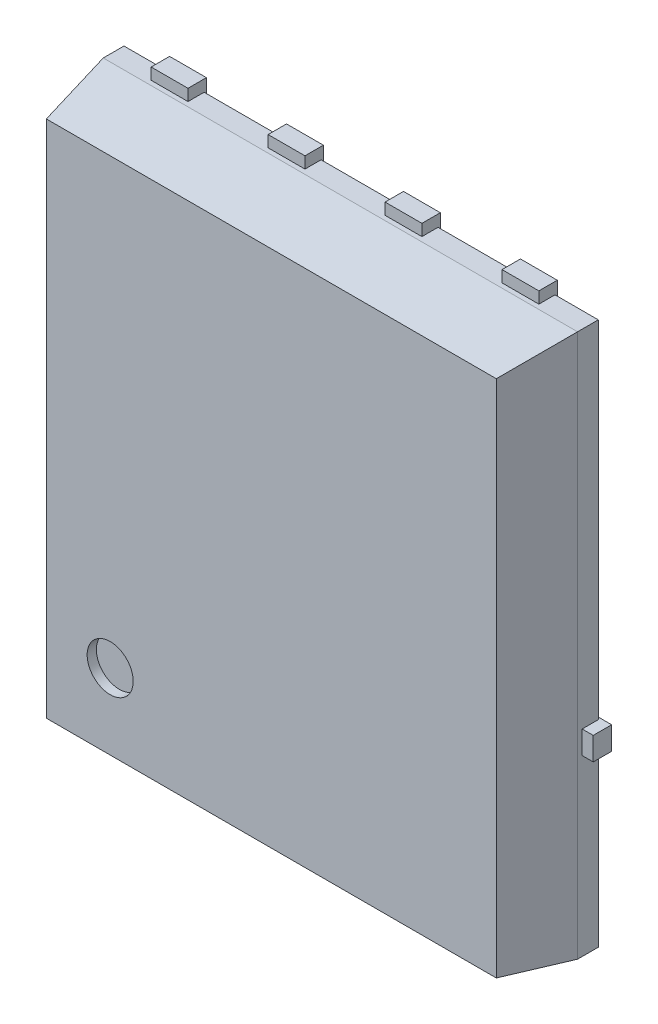
SolidWorks part; units mm, degrees
ref_plane "Plano frontal" through (0, 0, 0) normal (0, 0, 1) x (1, 0, 0)
ref_plane "Plano superior" through (0, 0, 0) normal (0, 1, 0) x (1, 0, 0)
ref_plane "Plano direito" through (0, 0, 0) normal (1, 0, 0) x (0, 0, -1)
sketch "Esboço3" plane through (0, 0, 0) normal (0, 0, 1) x (1, 0, 0)
  line L0 (0, -3.1767) -> (0, 3.1767) construction
  line L1 (-2.575, 2.95) -> (2.575, 2.95)
  line L2 (-2.575, 2.95) -> (-2.575, -2.95)
  line L3 (-2.575, -2.95) -> (2.575, -2.95)
  line L4 (2.575, 2.95) -> (2.575, -2.95)
  line L5 (3.0012, 0) -> (-2.8534, 0) construction
  point P7 (0, 0)
  point P8 (0, 2.95)
  point P11 (2.575, 0)
sketch "Esboço1" plane through (0, 0, 0) normal (0, 0, 1) x (1, 0, 0)
  line L0 (-0.435, 3.075) -> (-0.835, 3.075)
  line L1 (0, -3.5) -> (0, 3.5) construction
  line L2 (3.7953, 0) -> (-3.7953, 0) construction
  line L3 (4.6144, 3.075) -> (-4.6144, 3.075) construction
  line L4 (-1.705, 3.075) -> (-2.105, 3.075)
  line L5 (-0.435, 3.075) -> (-0.435, 2.775)
  line L6 (2.695, -1.06) -> (-2.695, -1.06)
  line L7 (-2.695, -1.06) -> (-2.695, -0.81)
  line L8 (3.5115, 2.525) -> (-3.5115, 2.525) construction
  line L9 (-0.835, 3.075) -> (-0.835, 2.775)
  line L10 (-1.085, 2.525) -> (-1.455, 2.525)
  line L11 (-1.705, 2.775) -> (-1.705, 3.075)
  line L12 (-2.105, 3.075) -> (-2.105, -0.56)
  line L13 (-2.355, -0.81) -> (-2.695, -0.81)
  line L14 (-0.185, 2.525) -> (0.185, 2.525)
  line L15 (2.355, -0.81) -> (2.695, -0.81)
  line L16 (2.105, 3.075) -> (2.105, -0.56)
  line L17 (1.705, 2.775) -> (1.705, 3.075)
  line L18 (1.085, 2.525) -> (1.455, 2.525)
  line L19 (0.835, 3.075) -> (0.835, 2.775)
  line L20 (2.695, -1.06) -> (2.695, -0.81)
  line L21 (0.435, 3.075) -> (0.435, 2.775)
  line L22 (1.705, 3.075) -> (2.105, 3.075)
  line L23 (0.435, 3.075) -> (0.835, 3.075)
  line L24 (0.435, -3.075) -> (0.835, -3.075)
  line L25 (1.705, -3.075) -> (2.105, -3.075)
  line L26 (-1.705, -3.075) -> (-2.105, -3.075)
  line L27 (-0.435, -3.075) -> (-0.835, -3.075)
  line L28 (-2.105, -3.075) -> (-2.105, -2.525)
  line L29 (-2.105, -2.525) -> (-1.705, -2.525)
  line L30 (-1.705, -2.525) -> (-1.705, -3.075)
  line L31 (-0.835, -3.075) -> (-0.835, -2.525)
  line L32 (-0.835, -2.525) -> (-0.435, -2.525)
  line L33 (-0.435, -2.525) -> (-0.435, -3.075)
  line L34 (0.435, -3.075) -> (0.435, -2.525)
  line L35 (0.435, -2.525) -> (0.835, -2.525)
  line L36 (0.835, -2.525) -> (0.835, -3.075)
  line L37 (1.705, -3.075) -> (1.705, -2.525)
  line L38 (1.705, -2.525) -> (2.105, -2.525)
  line L39 (2.105, -2.525) -> (2.105, -3.075)
  arc A0 (-2.105, -0.56) -> (-2.355, -0.81) centre (-2.355, -0.56) cw
  arc A1 (-0.435, 2.775) -> (-0.185, 2.525) centre (-0.185, 2.775) ccw
  arc A2 (-0.835, 2.775) -> (-1.085, 2.525) centre (-1.085, 2.775) cw
  arc A3 (-1.455, 2.525) -> (-1.705, 2.775) centre (-1.455, 2.775) cw
  arc A4 (1.455, 2.525) -> (1.705, 2.775) centre (1.455, 2.775) ccw
  arc A5 (0.835, 2.775) -> (1.085, 2.525) centre (1.085, 2.775) ccw
  arc A6 (0.435, 2.775) -> (0.185, 2.525) centre (0.185, 2.775) cw
  arc A7 (2.105, -0.56) -> (2.355, -0.81) centre (2.355, -0.56) ccw
  point P6 (0, 0)
  point P7 (0, 0)
  point P8 (-0.635, 3.075)
  point P11 (0, 3.075)
  point P14 (-1.905, 3.075)
  point P18 (0, -1.06)
  point P22 (0, 2.525)
  point P31 (-0.435, 2.525)
  point P34 (-0.835, 2.525)
  point P37 (-1.705, 2.525)
  point P50 (0, 2.525)
  point P55 (1.705, 2.525)
  point P56 (0.835, 2.525)
  point P57 (0.435, 2.525)
  dimension "D1" = 0.4
  dimension "D2" = 0.635
  dimension "D10" = 0.25
  dimension "D3" = 3.075
  dimension "D4" = 0.4
  dimension "D5" = 1.27
  dimension "D6" = 4.135
  dimension "D7" = 5.39
  dimension "D9" = 0.55
  dimension "D11" = 0.55
  dimension "D8" = 0.25
extrude "Pin Extrude" add sketch "Esboço1" along normal blind 0.2
extrude "Body" add sketch "Esboço3" along normal blind 0.75 draft 10 and the other way blind 0.225 from offset 0.25 separate body
sketch "Эскиз1" plane through (0, 0, 1) normal (0, 0, 1) x (1, 0, 0)
  circle A0 centre (-1.75, -2) radius 0.25
extrude "Вырез-Вытянуть1" cut sketch "Эскиз1" against normal blind 0.1
